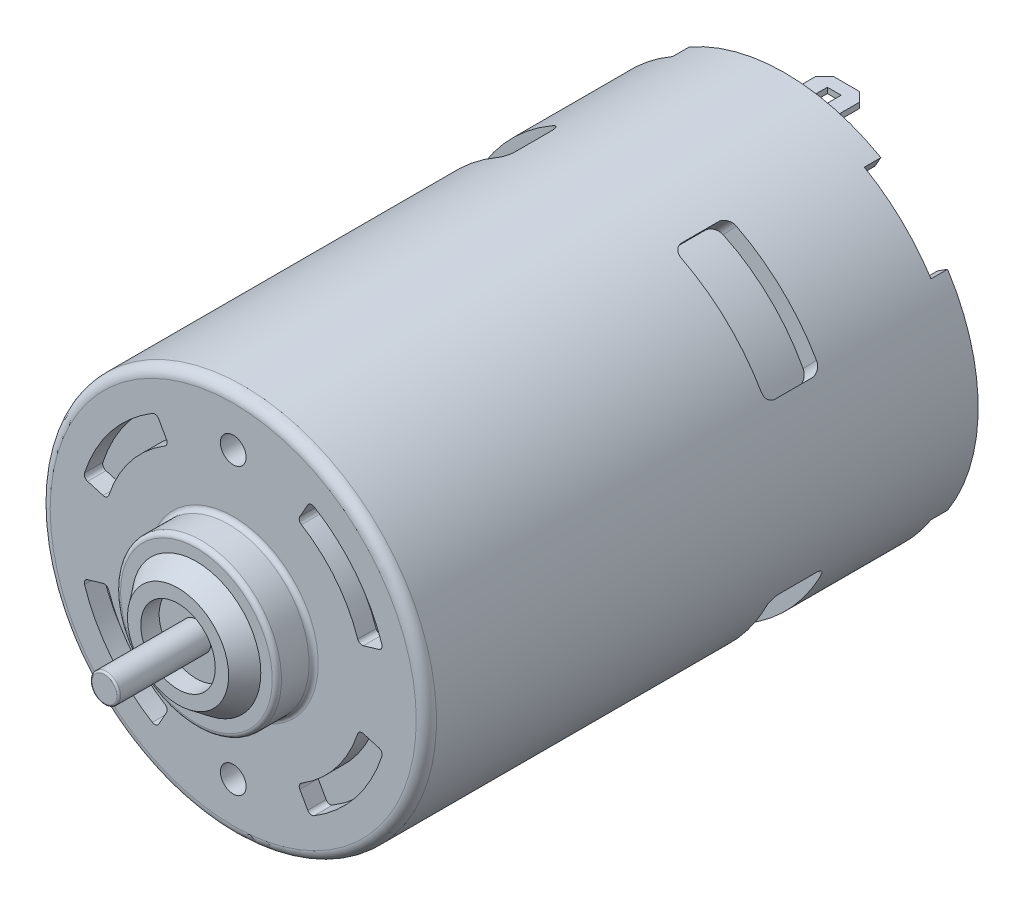
SolidWorks part; units mm, degrees
ref_plane "Plan de face" through (0, 0, 0) normal (0, 0, 1) x (1, 0, 0)
ref_plane "Plan de dessus" through (0, 0, 0) normal (0, 1, 0) x (1, 0, 0)
ref_plane "Plan de droite" through (0, 0, 0) normal (1, 0, 0) x (0, 0, -1)
sketch "Esquisse1" plane through (0, 0, 0) normal (1, 0, 0) x (0, 0, -1)
  line L0 (0, 0) -> (85, 0) construction
  line L1 (0, 0) -> (0, 1.55)
  line L2 (0, 1.55) -> (10, 1.55)
  line L3 (10, 4.05) -> (10, 1.55)
  line L4 (10, 4.05) -> (8, 4.05)
  line L5 (8, 4.05) -> (8, 5.5)
  line L6 (8, 5.5) -> (10, 7)
  line L7 (10, 7) -> (10, 8.75)
  line L8 (10, 8.75) -> (14, 8.75)
  line L9 (14, 8.75) -> (14, 21)
  line L10 (14, 21) -> (74, 21)
  line L11 (74, 21) -> (74, 8.75)
  line L12 (74, 8.75) -> (78, 8.75)
  line L13 (78, 8.75) -> (78, 6.5)
  line L14 (78, 6.5) -> (80.0183, 5.5)
  line L15 (80.0183, 5.5) -> (80.0183, 2.5)
  line L16 (80.0183, 2.5) -> (85, 2.5)
  line L17 (85, 2.5) -> (85, 0)
  line L18 (0, 0) -> (85, 0)
  dimension "D1" = 3.1
  dimension "D2" = 11
  dimension "D3" = 14
  dimension "D4" = 4
  dimension "D5" = 17.5
  dimension "D6" = 42
  dimension "D7" = 60
  dimension "D8" = 5
  dimension "D9" = 11
  dimension "D10" = 13
  dimension "D11" = 17.5
  dimension "D12" = 10
  dimension "D13" = 8
  dimension "D14" = 4.9817
  dimension "D15" = 7
  dimension "D16" = 6
  dimension "D17" = 85
  dimension "D18" = 4
  dimension "D19" = 2.5
revolve "Révolution1" add sketch "Esquisse1" angle 360 about L0
fillet "Congé1" radius 0.2 1 edges at (1.55, 0, 0)
fillet "Congé2" radius 0.5 1 edges at (8.75, 0, -10)
fillet "Congé3" radius 0.5 1 edges at (8.75, 0, -78)
fillet "Congé4" radius 0.5 1 edges at (8.75, 0, -74)
fillet "Congé5" radius 1.1 1 edges at (21, 0, -14)
fillet "Congé6" radius 0.5 1 edges at (8.75, 0, -14)
sketch "Esquisse2" plane through (0, 0, -74) normal (0, 0, -1) x (-1, 0, 0)
  line L0 (-26.0367, 21) -> (19.8457, 21) construction
  line L1 (-8.5, -12.3) -> (8.5, -12.3)
  line L2 (-26.0367, -21) -> (21.5815, -21) construction
  line L3 (0, -21) -> (0, -24.1895) construction
  line L4 (-7.5, 14.3) -> (7.5, 14.3)
  line L5 (7.5, 18.2165) -> (7.5, 14.3)
  line L6 (-12, 21) -> (-23.2409, 14.9243)
  line L7 (-7.5, 18.2165) -> (-7.5, 14.3)
  line L8 (-7.5, -14.3) -> (-7.5, -18.2165)
  line L9 (7.5, -14.3) -> (7.5, -18.2165)
  line L10 (-7.5, -14.3) -> (7.5, -14.3)
  line L11 (0, 14.3) -> (0, -14.3) construction
  line L12 (12, 21) -> (12, 20.974)
  line L13 (-8.5, 12.3) -> (8.5, 12.3)
  line L14 (12, 20.974) -> (9.7831, 17.0992)
  line L15 (-9.7831, -17.0992) -> (-13.4858, -23.5709)
  line L16 (9.7739, -17.1044) -> (12.316, -21.553)
  line L17 (-12, 21) -> (-9.7739, 17.1044)
  line L18 (-13.4858, -23.5709) -> (-22.5762, -14.4805)
  line L19 (-8.5, 15.5255) -> (-8.5, 12.3)
  line L20 (8.5, 15.5255) -> (8.5, 12.3)
  line L21 (-8.5, -12.3) -> (-8.5, -15.5255)
  line L22 (8.5, -12.3) -> (8.5, -15.5255)
  line L23 (-23.2409, 14.9243) -> (-16.5765, 10.6447)
  line L24 (25.4965, 16.3535) -> (16.5822, 10.6359)
  line L25 (16.5765, -10.6447) -> (23.5589, -15.1285)
  line L26 (-16.5822, -10.6359) -> (-22.5762, -14.4805)
  line L27 (12.316, -21.553) -> (23.5589, -15.1285)
  line L29 (25.4965, 16.3535) -> (12, 21)
  arc A0 (-7.5, 18.2165) -> (-9.7739, 17.1044) centre (0, 0) ccw
  circle A1 centre (0, 0) radius 21 construction
  arc A2 (-8.5, 15.5255) -> (-8.5, -15.5255) centre (0, 0) ccw
  arc A3 (7.5, -18.2165) -> (9.7739, -17.1044) centre (0, 0) ccw
  arc A4 (8.5, -15.5255) -> (8.5, 15.5255) centre (0, 0) ccw
  arc A5 (-16.5765, 10.6447) -> (-16.5822, -10.6359) centre (0, 0) ccw
  arc A6 (-9.7831, -17.0992) -> (-7.5, -18.2165) centre (0, 0) ccw
  arc A7 (16.5765, -10.6447) -> (16.5822, 10.6359) centre (0, 0) ccw
  arc A8 (9.7831, 17.0992) -> (7.5, 18.2165) centre (0, 0) ccw
  point P1 (10.4189, -18.2331)
  point P41 (17.6704, -11.3472)
  point P42 (-17.6764, -11.3377)
  point P48 (-10.4286, -18.2275)
  dimension "D1" = 1.3
  dimension "D2" = 2
  dimension "D3" = 2
  dimension "D4" = 2
  dimension "D9" = 10
  dimension "D10" = 10
extrude "Enlèv. mat.-Extru.1" cut sketch "Esquisse2" against normal blind 1.8
fillet "Congé7" radius 1.5 4 edges at (8.5, -15.5255, -73.1) (-8.5, -15.5255, -73.1) (-8.5, 15.5255, -73.1) (8.5, 15.5255, -73.1)
fillet "Congé8" radius 1.5 12 edges at (-8.5, 12.5226, -74) (-9.3438, 14.0941, -74) (0, 12.3, -74) (9.3438, 14.0941, -74) (8.5, 12.5226, -74) (-17.7, 0, -74) (-9.3438, -14.0941, -74) (-8.5, -12.5226, -74) (9.3438, -14.0941, -74) (8.5, -12.5226, -74) (0, -12.3, -74) (17.7, 0, -74)
sketch "Esquisse3" plane through (0, 0, -74) normal (0, 0, -1) x (-1, 0, 0)
  line L0 (-14.6437, 3.25) -> (-10.5089, 3.25)
  line L1 (14.6437, -3.25) -> (10.5089, -3.25)
  line L2 (10.5089, 3.25) -> (14.6437, 3.25)
  line L3 (-10.5089, -3.25) -> (-14.6437, -3.25)
  line L4 (0, 33.3432) -> (0, -33.3432) construction
  line L5 (-24.6699, -11) -> (41.6924, -11) construction
  line L6 (-35.9052, 11) -> (40.0189, 11) construction
  line L7 (-10.198, 11) -> (-8.7963, 6.6049)
  line L8 (0.0056, 21) -> (0, 20.9824)
  line L9 (8.7963, 6.6049) -> (10.198, 11)
  line L10 (8.7976, -6.6032) -> (10.198, -11)
  line L11 (-8.7965, -6.6046) -> (-10.198, -11)
  arc A0 (-14.6437, -3.25) -> (-10.198, -11) centre (0, 0) ccw
  arc A1 (-10.5089, -3.25) -> (-8.7965, -6.6046) centre (0, 0) ccw
  arc A2 (10.5089, 3.25) -> (8.7963, 6.6049) centre (0, 0) ccw
  arc A3 (14.6437, 3.25) -> (10.198, 11) centre (0, 0) ccw
  arc A4 (10.4286, 18.2275) -> (-10.4189, 18.2331) centre (0, 0) ccw construction
  arc A5 (-10.198, 11) -> (-14.6437, 3.25) centre (0, 0) ccw
  arc A6 (-8.7963, 6.6049) -> (-10.5089, 3.25) centre (0, 0) ccw
  arc A7 (10.198, -11) -> (14.6437, -3.25) centre (0, 0) ccw
  arc A8 (8.7976, -6.6032) -> (10.5089, -3.25) centre (0, 0) ccw
  point P12 (0.0056, 21)
  point P13 (0, -20.9759)
  point P21 (0, 11)
  point P22 (0, 11)
  point P23 (10.198, 11)
  point P24 (-10.198, 11)
  dimension "D1" = 30
  dimension "D2" = 22
  dimension "D3" = 3.25
  dimension "D4" = 6.5
extrude "Enlèv. mat.-Extru.3" cut sketch "Esquisse3" against normal blind 4 contours A1 L3 A0 L11 | A6 L7 A5 L0 | L2 A3 L9 A2 | A8 L10 A7 L1
fillet "Congé9" radius 1 16 edges at (14.6437, -3.25, -72) (10.5089, 3.25, -72) (-14.6437, 3.25, -72) (8.7963, 6.6049, -72) (8.7965, -6.6046, -72) (10.198, -11, -72) (-14.6437, -3.25, -72) (-10.198, -11, -72) (-8.7976, -6.6032, -72) (14.6437, 3.25, -72) (-10.5089, 3.25, -72) (-8.7963, 6.6049, -72) (10.5089, -3.25, -72) (-10.5089, -3.25, -72) (-10.198, 11, -72) (10.198, 11, -72)
sketch "Esquisse4" plane through (0, 0, -74) normal (0, 0, -1) x (-1, 0, 0)
  line L0 (-7.5, 18.2165) -> (-7.5, 14.3)
  line L1 (7.5, -18.2165) -> (7.5, -14.3)
  line L2 (-7.5, 14.3) -> (7.5, 14.3)
  line L3 (7.5, -14.3) -> (-7.5, -14.3)
  line L4 (-7.5, -14.3) -> (-7.5, -18.2165)
  line L5 (7.5, 14.3) -> (7.5, 18.2165)
  line L6 (6.5, -15.3) -> (-6.5, -15.3)
  line L7 (-6.5, -15.3) -> (-6.5, -17.534)
  line L8 (6.5, -17.534) -> (6.5, -15.3)
  line L9 (-6.5, 17.534) -> (-6.5, 15.3)
  line L10 (-6.5, 15.3) -> (6.5, 15.3)
  line L11 (6.5, 15.3) -> (6.5, 17.534)
  arc A0 (7.5, 18.2165) -> (-7.5, 18.2165) centre (0, 0) ccw
  arc A1 (-7.5, -18.2165) -> (7.5, -18.2165) centre (0, 0) ccw
  arc A2 (-6.5, -17.534) -> (6.5, -17.534) centre (0, 0) ccw
  arc A3 (6.5, 17.534) -> (-6.5, 17.534) centre (0, 0) ccw
  dimension "D1" = 1
extrude "Boss.-Extru.1" add sketch "Esquisse4" along normal blind 0.6
sketch "Esquisse5" plane through (0, 0, -74) normal (0, 0, -1) x (-1, 0, 0)
  line L0 (2.4, -16) -> (2.4, -16.6)
  line L4 (-2.4, 16) -> (2.4, 16)
  line L5 (-2.4, -16.6) -> (2.4, -16.6)
  line L6 (-2.4, 16.6) -> (2.4, 16.6)
  line L7 (-2.4, -16) -> (2.4, -16)
  line L8 (-2.4, 16.6) -> (-2.4, 16)
  line L9 (2.4, 16.6) -> (2.4, 16)
  line L10 (-2.4, -16) -> (-2.4, -16.6)
  point P0 (-5.7614, 16.3)
  point P1 (5.1735, 16.3)
  point P2 (-5.7614, -16.3)
  point P3 (5.8789, -16.3)
  point P8 (-5.7614, 16)
  point P9 (5.1735, 16)
  point P10 (-5.7614, -16.6)
  point P11 (5.8789, -16.6)
  point P12 (-5.7614, 16.6)
  point P13 (5.1735, 16.6)
  point P14 (-5.7614, -16)
  point P15 (5.8789, -16)
  dimension "D5" = 2.4
  dimension "D6" = 2.4
extrude "Boss.-Extru.2" add sketch "Esquisse5" along normal blind 7
sketch "Esquisse6" plane through (0, -16.6, 0) normal (0, -1, 0) x (1, 0, 0)
  line L0 (2.4, -81) -> (2.4, -74) construction
  line L1 (-0.75, -76.85) -> (0.75, -76.85)
  line L2 (-0.75, -76.85) -> (-0.75, -79.35)
  line L3 (-0.75, -79.35) -> (0.75, -79.35)
  line L4 (0.75, -76.85) -> (0.75, -79.35)
  line L5 (-2.4, -81) -> (-2.4, -74) construction
  line L6 (2.4, -81) -> (-2.4, -81) construction
  dimension "D1" = 2.5
  dimension "D2" = 1.5
  dimension "D3" = 1.65
  dimension "D4" = 1.65
  dimension "D5" = 1.65
extrude "Enlèv. mat.-Extru.4" cut sketch "Esquisse6" against normal up to next
sketch "Esquisse7" plane through (0, 16.6, 0) normal (0, 1, 0) x (1, 0, 0)
  line L0 (-2.4, 81) -> (-2.4, 74) construction
  line L1 (-0.75, 79.35) -> (0.75, 79.35)
  line L2 (-0.75, 79.35) -> (-0.75, 76.85)
  line L3 (-0.75, 76.85) -> (0.75, 76.85)
  line L4 (0.75, 79.35) -> (0.75, 76.85)
  line L5 (-2.4, 81) -> (2.4, 81) construction
  point P6 (0, 81)
  dimension "D1" = 1.5
  dimension "D2" = 2.5
  dimension "D3" = 1.65
  dimension "D4" = 1.65
extrude "Enlèv. mat.-Extru.5" cut sketch "Esquisse7" against normal blind 7
chamfer "Chanfrein1" distance 1.3 angle 45 4 edges at (2.4, 16.3, -81) (-2.4, 16.3, -81) (2.4, -16.3, -81) (-2.4, -16.3, -81)
chamfer "Chanfrein2" distance 0.3 angle 45 1 edges at (0, 16.6, -81)
chamfer "Chanfrein3" distance 0.3 angle 45 1 edges at (0, -16.6, -81)
fillet "Congé10" radius 0.3 1 edges at (2.5, 0, -85)
ref_plane "plan 104" through (14.4004, 15.2849, 0) normal (0.6857, 0.7279, 0) x (0, 0, 1)
ref_plane "Plan4" through (-14.5285, 15.1632, 0) normal (-0.6918, 0.7221, 0) x (0, 0, 1)
ref_plane "Plan5" through (-14.4004, -15.2849, 0) normal (-0.6857, -0.7279, 0) x (0, 0, 1)
sketch "Esquisse8" plane through (14.4004, 15.2849, 0) normal (0.6857, 0.7279, 0) x (0, 0, 1)
  line L0 (-72.2, 0.0804) -> (5.2158, 0.0804) construction
  line L1 (-59.2, -6.9196) -> (-53.2, -6.9196)
  line L2 (-59.2, -6.9196) -> (-59.2, 7.0804)
  line L3 (-59.2, 7.0804) -> (-53.2, 7.0804)
  line L4 (-53.2, -6.9196) -> (-53.2, 7.0804)
  line L5 (-72.2, 5.0804) -> (-72.2, -4.9196) construction
  point P8 (-59.2, 0.0804)
  dimension "D1" = 14
  dimension "D2" = 6
  dimension "D3" = 13
extrude "Enlèv. mat.-Extru.6" cut sketch "Esquisse8" against normal offset from surface (3.3048 mm away) 2
fillet "Congé11" radius 1 4 edges at (7.8287, 18.4004, -59.2) (7.8287, 18.4004, -53.2) (17.9773, 8.7563, -53.2) (17.9773, 8.7563, -59.2)
pattern_circular "Répétition circulaire1" count 4 over 360 about axis through (0, 0, 0) along (0, 0, 1) of "Congé11", "Enlèv. mat.-Extru.6"
sketch "Esquisse9" plane through (0, 0, -14) normal (0, 0, 1) x (1, 0, 0)
  line L0 (8.3509, -14.8075) -> (7, -12.4122)
  line L1 (-7, -12.4122) -> (-8.3509, -14.8075)
  line L2 (-13.6771, -4) -> (-16.3165, -4.7719)
  line L3 (13.6771, -4) -> (16.3165, -4.7719)
  line L4 (0, 32.9703) -> (0, -38.9775) construction
  line L5 (8.3509, 14.8075) -> (7, 12.4122)
  line L6 (-13.6771, 4) -> (-16.3165, 4.7719)
  line L7 (16.3165, 4.7719) -> (13.6771, 4)
  line L8 (-7, 12.4122) -> (-8.3509, 14.8075)
  arc A0 (-13.6771, -4) -> (-7, -12.4122) centre (0, 0) ccw
  arc A1 (-16.3165, -4.7719) -> (-8.3509, -14.8075) centre (0, 0) ccw
  arc A2 (-7, 12.4122) -> (-13.6771, 4) centre (0, 0) ccw
  arc A3 (-8.3509, 14.8075) -> (-16.3165, 4.7719) centre (0, 0) ccw
  arc A4 (8.3509, -14.8075) -> (16.3165, -4.7719) centre (0, 0) ccw
  arc A5 (7, -12.4122) -> (13.6771, -4) centre (0, 0) ccw
  arc A6 (16.3165, 4.7719) -> (8.3509, 14.8075) centre (0, 0) ccw
  arc A7 (13.6771, 4) -> (7, 12.4122) centre (0, 0) ccw
  circle A9 centre (0, 15.5) radius 1.4
  circle A10 centre (0, -15.5) radius 1.4
  point P8 (0, 15.5)
  point P13 (7, 12.4122)
  point P14 (13.6771, 4)
  point P15 (13.6771, -4)
  point P16 (7, -12.4122)
  point P17 (-7, -12.4122)
  point P18 (-13.6771, 4)
  point P19 (-13.6771, -4)
  point P27 (0, -15.5)
  dimension "D6" = 17
  dimension "D2" = 2.8
  dimension "D3" = 2.8
extrude "Enlèv. mat.-Extru.7" cut sketch "Esquisse9" against normal blind 2
fillet "Congé12" radius 0.5 16 edges at (-7, -12.4122, -15) (-13.6771, -4, -15) (-8.3509, -14.8075, -15) (-16.3165, -4.7719, -15) (7, -12.4122, -15) (16.3165, -4.7719, -15) (13.6771, -4, -15) (8.3509, -14.8075, -15) (13.6771, 4, -15) (16.3165, 4.7719, -15) (8.3509, 14.8075, -15) (7, 12.4122, -15) (-16.3165, 4.7719, -15) (-13.6771, 4, -15) (-7, 12.4122, -15) (-8.3509, 14.8075, -15)
